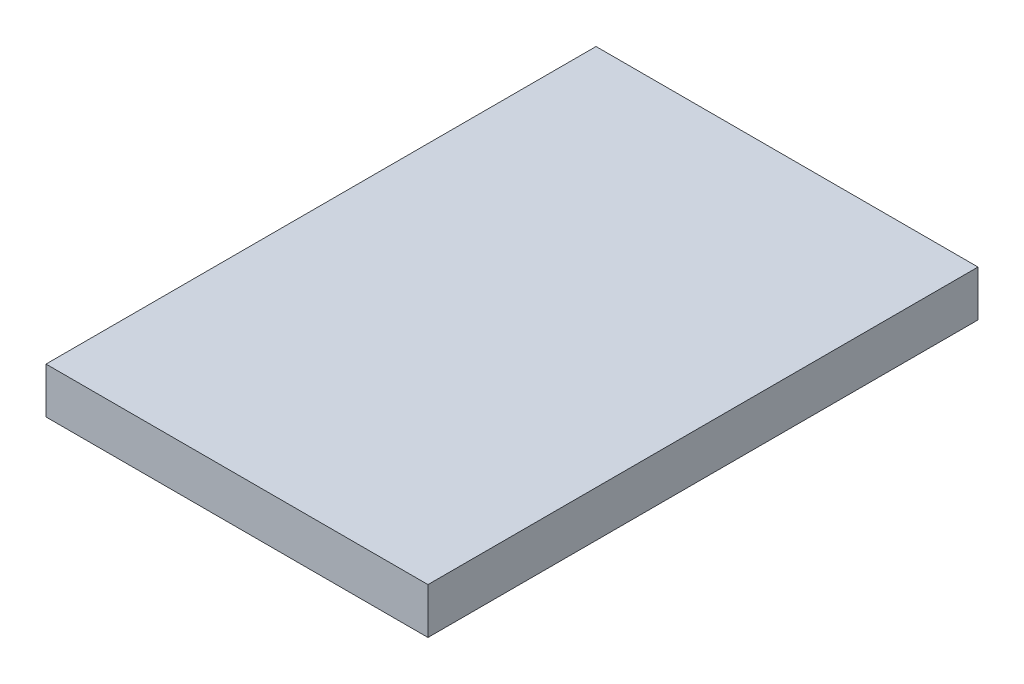
SolidWorks part; units mm, degrees
ref_plane "前视基准面" through (0, 0, 0) normal (0, 0, 1) x (1, 0, 0)
ref_plane "上视基准面" through (0, 0, 0) normal (0, 1, 0) x (1, 0, 0)
ref_plane "右视基准面" through (0, 0, 0) normal (1, 0, 0) x (0, 0, -1)
sketch "草图1" plane through (0, 0, 0) normal (0, 1, 0) x (1, 0, 0)
  line L1 (-12.5, 18) -> (12.5, 18)
  line L2 (-12.5, 18) -> (-12.5, -18)
  line L3 (-12.5, -18) -> (12.5, -18)
  line L4 (12.5, 18) -> (12.5, -18)
  line L5 (-12.5, 18) -> (12.5, -18) construction
  line L6 (-12.5, -18) -> (12.5, 18) construction
  point P0 (0, 0)
  dimension "D1" = 36
  dimension "D2" = 25
extrude "凸台-拉伸1" add sketch "草图1" along normal blind 3
